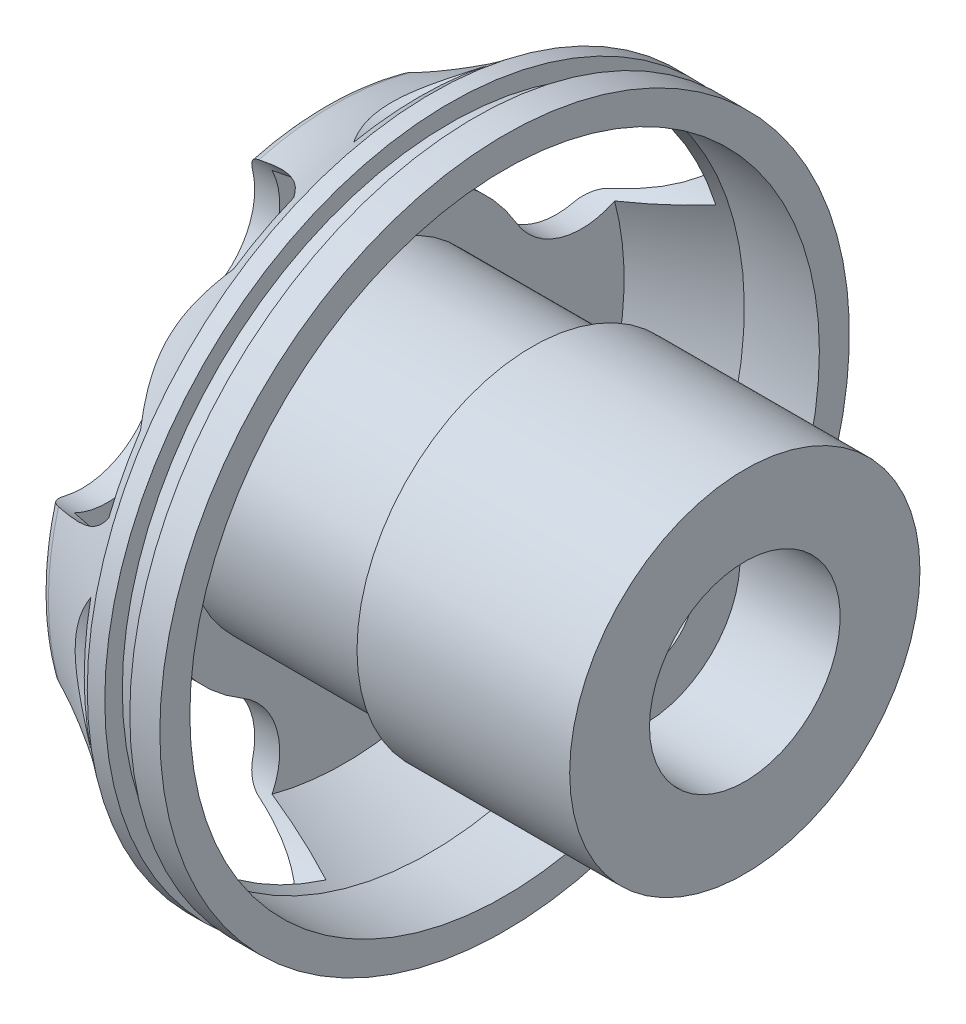
SolidWorks part; units mm, degrees
ref_plane "Front Plane" through (0, 0, 0) normal (0, 0, 1) x (1, 0, 0)
ref_plane "Top Plane" through (0, 0, 0) normal (0, 1, 0) x (1, 0, 0)
ref_plane "Right Plane" through (0, 0, 0) normal (1, 0, 0) x (0, 0, -1)
sketch "Sketch1" plane through (0, 0, 0) normal (0, 0, 1) x (1, 0, 0)
  line L0 (0, 18.0576) -> (0, 0) construction
  line L1 (0, 0) -> (33.6629, 0) construction
  line L2 (17, 3.81) -> (13, 3.81)
  line L3 (13, 3.81) -> (13, 2)
  line L4 (13, 2) -> (4, 2)
  line L5 (4, 2) -> (4, 3.81)
  line L6 (4, 3.81) -> (0, 3.81)
  line L7 (0, 3.81) -> (0, 11.176)
  line L8 (4.5, 13.7795) -> (5.2, 13.7795)
  line L9 (7.4, 13.7795) -> (7.4, 12.5795)
  line L10 (7.4, 12.5795) -> (4.4, 12.5795)
  line L11 (4.4, 12.5795) -> (1, 11.176)
  line L12 (1, 11.176) -> (1, 6.35)
  line L13 (1, 6.35) -> (8.5, 6.35)
  line L14 (8.5, 6.35) -> (8.5, 7)
  line L15 (8.5, 7) -> (17, 7)
  line L16 (17, 7) -> (17, 3.81)
  line L17 (6.2, 13.7795) -> (7.4, 13.7795)
  line L19 (5.2, 13.7795) -> (5.2, 13.0795)
  line L20 (5.2, 13.0795) -> (6.2, 13.0795)
  line L21 (6.2, 13.7795) -> (6.2, 13.0795)
  arc A1 (0, 11.176) -> (4.5, 13.7795) centre (-6.791, 28.1047) ccw
  dimension "D19" = 18.24
  dimension "D1" = 13.7795
  dimension "D2" = 17
  dimension "D3" = 2
  dimension "D4" = 4
  dimension "D5" = 1
  dimension "D6" = 7
  dimension "D7" = 6.35
  dimension "D8" = 4.5
  dimension "D9" = 3.81
  dimension "D10" = 2.9
  dimension "D11" = 3
  dimension "D12" = 4.5
  dimension "D13" = 1.2
  dimension "D14" = 11.176
  dimension "D15" = 4.826
  dimension "D16" = 0.7
  dimension "D17" = 1
  dimension "D18" = 0.7
revolve "Revolve1" add sketch "Sketch1" angle 360 about L1
fillet "Fillet1" radius 1 1 edges at (0, 0, 11.176)
sketch "Sketch2" plane through (0, 0, 0) normal (-1, 0, 0) x (0, 0, 1)
  line L0 (21.2806, 0) -> (0, 0) construction
  line L1 (0, 0) -> (0, 19.6679) construction
  line L2 (0, 0) -> (17.9851, 17.9851) construction
  arc A0 (9.4757, 5.5866) -> (5.5866, 9.4757) centre (0, 0) ccw construction
  arc A1 (12.06, 7.1103) -> (7.1103, 12.06) centre (0, 0) ccw
  arc A2 (6.8914, 4.063) -> (4.063, 6.8914) centre (0, 0) ccw
  arc A3 (6.8914, 4.063) -> (12.06, 7.1103) centre (9.4757, 5.5866) ccw
  arc A4 (7.1103, 12.06) -> (4.063, 6.8914) centre (5.5866, 9.4757) ccw
  arc A5 (4.063, -6.8914) -> (6.8914, -4.063) centre (0, 0) ccw
  arc A6 (4.063, -6.8914) -> (7.1103, -12.06) centre (5.5866, -9.4757) ccw
  arc A7 (12.06, -7.1103) -> (6.8914, -4.063) centre (9.4757, -5.5866) ccw
  arc A8 (7.1103, -12.06) -> (12.06, -7.1103) centre (0, 0) ccw
  arc A9 (5.5866, -9.4757) -> (9.4757, -5.5866) centre (0, 0) ccw construction
  arc A10 (-6.8914, -4.063) -> (-4.063, -6.8914) centre (0, 0) ccw
  arc A11 (-6.8914, -4.063) -> (-12.06, -7.1103) centre (-9.4757, -5.5866) ccw
  arc A12 (-7.1103, -12.06) -> (-4.063, -6.8914) centre (-5.5866, -9.4757) ccw
  arc A13 (-12.06, -7.1103) -> (-7.1103, -12.06) centre (0, 0) ccw
  arc A14 (-9.4757, -5.5866) -> (-5.5866, -9.4757) centre (0, 0) ccw construction
  arc A15 (-4.063, 6.8914) -> (-6.8914, 4.063) centre (0, 0) ccw
  arc A16 (-4.063, 6.8914) -> (-7.1103, 12.06) centre (-5.5866, 9.4757) ccw
  arc A17 (-12.06, 7.1103) -> (-6.8914, 4.063) centre (-9.4757, 5.5866) ccw
  arc A18 (-7.1103, 12.06) -> (-12.06, 7.1103) centre (0, 0) ccw
  arc A19 (-5.5866, 9.4757) -> (-9.4757, 5.5866) centre (0, 0) ccw construction
  arc A20 (7.1964, 11.751) -> (11.751, 7.1964) centre (14.0188, 14.0188) ccw
  circle A21 centre (0, 0) radius 13.7795 construction
  arc A22 (13.3978, 3.2206) -> (13.3978, -3.2206) centre (19.8256, 0) ccw
  arc A23 (11.751, -7.1964) -> (7.1964, -11.751) centre (14.0188, -14.0188) ccw
  arc A24 (3.2206, -13.3978) -> (-3.2206, -13.3978) centre (0, -19.8256) ccw
  arc A25 (-7.1964, -11.751) -> (-11.751, -7.1964) centre (-14.0188, -14.0188) ccw
  arc A26 (-13.3978, -3.2206) -> (-13.3978, 3.2206) centre (-19.8256, 0) ccw
  arc A27 (-11.751, 7.1964) -> (-7.1964, 11.751) centre (-14.0188, 14.0188) ccw
  arc A28 (-3.2206, 13.3978) -> (3.2206, 13.3978) centre (0, 19.8256) ccw
  arc A29 (3.2206, 13.3978) -> (-3.2206, 13.3978) centre (0, 0) ccw
  arc A30 (-7.1964, 11.751) -> (-11.751, 7.1964) centre (0, 0) ccw
  arc A31 (11.751, 7.1964) -> (7.1964, 11.751) centre (0, 0) ccw
  arc A32 (13.3978, -3.2206) -> (13.3978, 3.2206) centre (0, 0) ccw
  arc A33 (7.1964, -11.751) -> (11.751, -7.1964) centre (0, 0) ccw
  arc A34 (-3.2206, -13.3978) -> (3.2206, -13.3978) centre (0, 0) ccw
  arc A35 (-11.751, -7.1964) -> (-7.1964, -11.751) centre (0, 0) ccw
  arc A36 (-13.3978, 3.2206) -> (-13.3978, -3.2206) centre (0, 0) ccw
  point P7 (7.7782, 7.7782)
  point P17 (7.7782, -7.7782)
  point P24 (-7.7782, -7.7782)
  point P31 (-7.7782, 7.7782)
  dimension "D3" = 14
  dimension "D4" = 8
  dimension "D1" = 45
  dimension "D2" = 5.5
  dimension "D5" = 4
  dimension "D6" = 8
extrude "Cut-Extrude3" cut sketch "Sketch2" against normal blind 4
sketch "Sketch3" plane through (0, 0, 0) normal (-1, 0, 0) x (0, 0, 1)
  circle A0 centre (0, 0) radius 4.4577 construction
  circle A1 centre (0, 0) radius 4.4577 construction
  circle A2 centre (4.4577, 0) radius 1.524
  circle A3 centre (-4.4577, 0) radius 1.524
  circle A4 centre (0, -4.4577) radius 1.524
  circle A5 centre (0, 4.4577) radius 1.524
  dimension "D1" = 8.9154
  dimension "D2" = 8.9154
  dimension "D3" = 3.048
extrude "Cut-Extrude4" cut sketch "Sketch3" against normal blind 4
